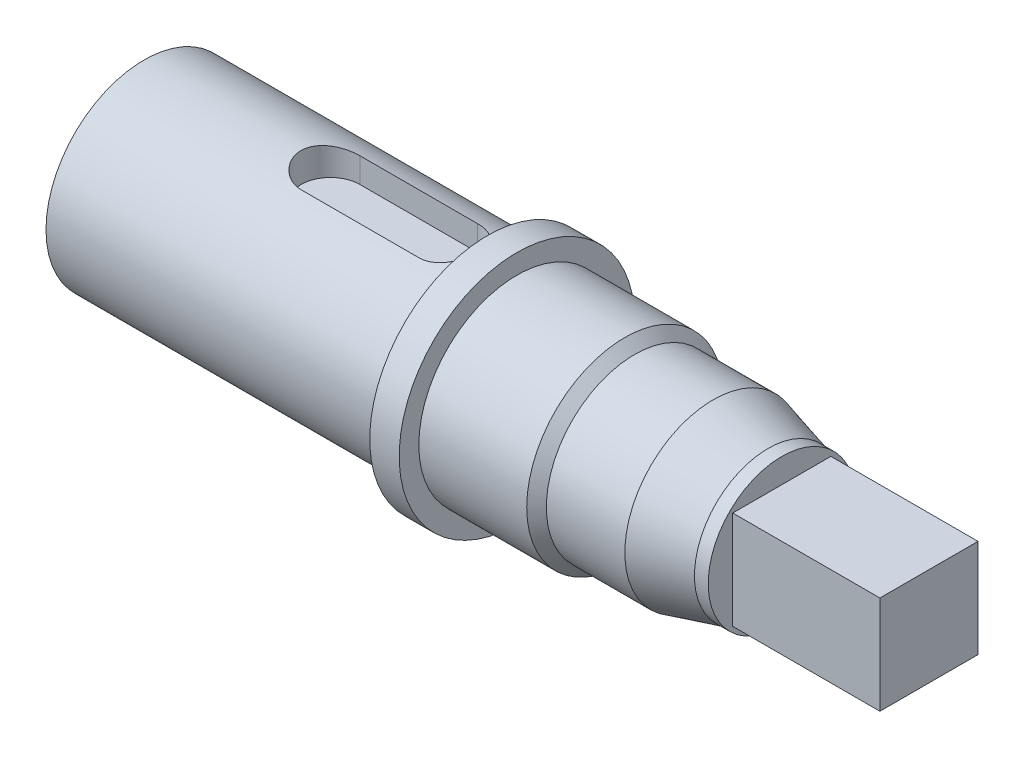
SolidWorks part; units mm, degrees
material "Сталь 40Х ГОСТ 4543-71"
ref_plane "Plane1" through (0, 0, 0) normal (0, 0, 1) x (1, 0, 0)
ref_plane "Plane2" through (0, 0, 0) normal (0, 1, 0) x (1, 0, 0)
ref_plane "Plane3" through (0, 0, 0) normal (1, 0, 0) x (0, 0, -1)
sketch "Эскиз1" plane through (0, 0, 0) normal (0, 0, 1) x (1, 0, 0)
  line L0 (0, 0) -> (-54.3181, 0) construction
  line L1 (-25, 10) -> (10, 10)
  line L2 (24, 10) -> (25, 9)
  line L3 (10, 10) -> (10, 12)
  line L4 (10, 12) -> (13, 12)
  line L5 (13, 12) -> (13, 10)
  line L6 (13, 10) -> (24, 10)
  line L7 (25, 9) -> (33, 9)
  line L8 (33, 9) -> (38.5981, 7.5)
  line L9 (38.5981, 7.5) -> (55, 7.5)
  line L10 (55, 7.5) -> (55, 0)
  line L13 (-25, 10) -> (-25, 0)
  line L14 (-25, 0) -> (55, 0)
  dimension "D1" = 35
  dimension "D2" = 20
  dimension "D3" = 10
  dimension "D4" = 24
  dimension "D5" = 3
  dimension "D6" = 11
  dimension "D7" = 45
  dimension "D8" = 18
  dimension "D9" = 15
  dimension "D10" = 15
  dimension "D11" = 20
  dimension "D12" = 45
revolve "Повернуть1" add sketch "Эскиз1" angle 360 about L0
sketch "Эскиз2" plane through (55, 0, 0) normal (1, 0, 0) x (0, 0, -1)
  line L1 (-5, -5) -> (5, -5)
  line L2 (-5, -5) -> (-5, 5)
  line L3 (-5, 5) -> (5, 5)
  line L4 (5, -5) -> (5, 5)
  line L5 (-5, -5) -> (5, 5) construction
  line L6 (-5, 5) -> (5, -5) construction
  point P0 (0, 0)
  dimension "D1" = 10
extrude "Вырез-Вытянуть1" cut sketch "Эскиз2" against normal blind 15 flip side to cut
sketch "Эскиз3" plane through (0, 0, 0) normal (0, 1, 0) x (1, 0, 0)
  line L0 (-6, 0) -> (6, 0) construction
  line L1 (-6, 3) -> (6, 3)
  line L2 (-6, -3) -> (6, -3)
  arc A0 (-6, 3) -> (-6, -3) centre (-6, 0) ccw
  arc A1 (6, -3) -> (6, 3) centre (6, 0) ccw
  point P2 (0, 0)
  dimension "D2" = 18
  dimension "D1" = 6
extrude "Вырез-Вытянуть2" cut sketch "Эскиз3" along normal through all from offset 7
